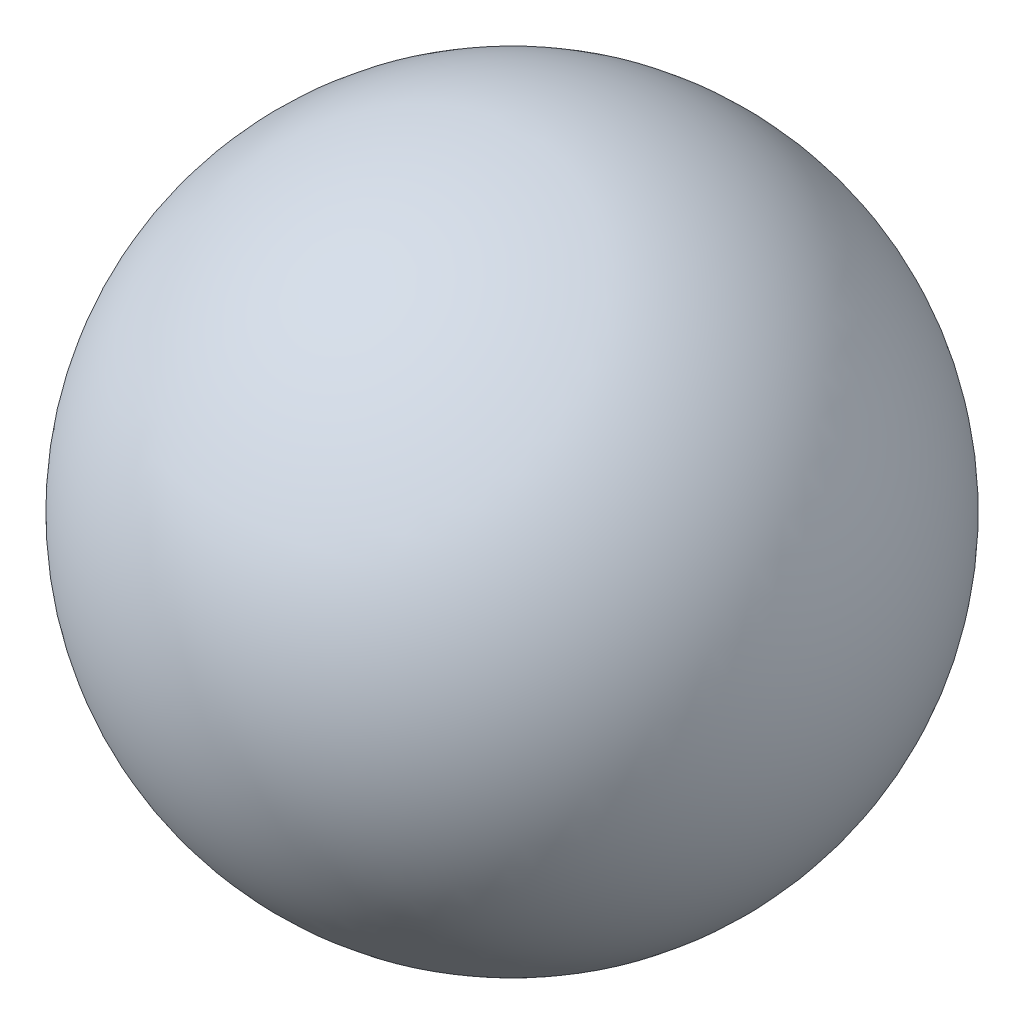
SolidWorks part; units mm, degrees
material "Caoutchouc"
ref_plane "Plan de face" through (0, 0, 0) normal (0, 0, 1) x (1, 0, 0)
ref_plane "Plan de dessus" through (0, 0, 0) normal (0, 1, 0) x (1, 0, 0)
ref_plane "Plan de droite" through (0, 0, 0) normal (1, 0, 0) x (0, 0, -1)
sketch "Esquisse1" plane through (0, 0, 0) normal (0, 0, 1) x (1, 0, 0)
  line L0 (0, 20) -> (0, -20) construction
  line L1 (0, 20) -> (0, -20)
  arc A0 (0, 20) -> (0, -20) centre (0, 0) ccw
  dimension "D1" = 20
revolve "Révolution1" add sketch "Esquisse1" angle 360 about L0
